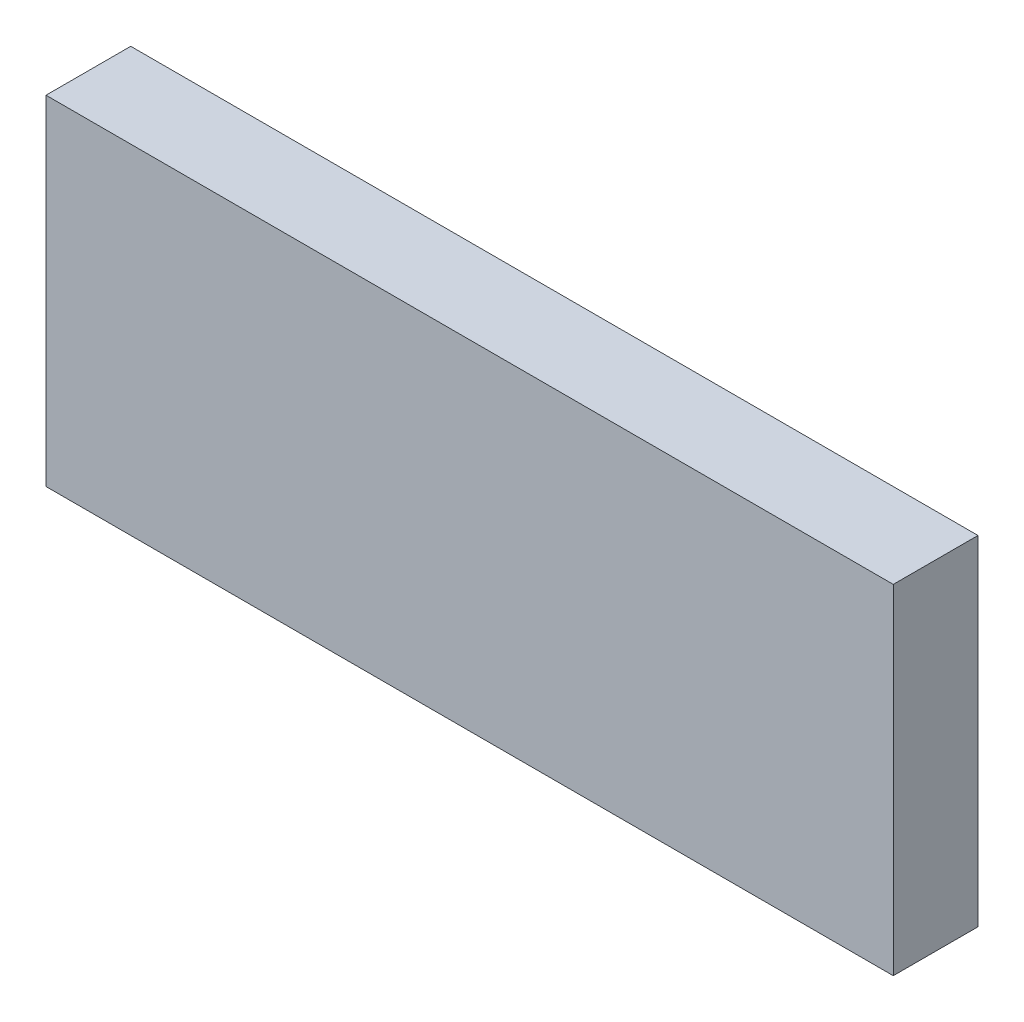
SolidWorks part; units mm, degrees
ref_plane "Front Plane" through (0, 0, 0) normal (0, 0, 1) x (1, 0, 0)
ref_plane "Top Plane" through (0, 0, 0) normal (0, 1, 0) x (1, 0, 0)
ref_plane "Right Plane" through (0, 0, 0) normal (1, 0, 0) x (0, 0, -1)
sketch "Sketch2" plane through (0, 0, 0) normal (0, 0, 1) x (1, 0, 0)
  line L1 (0, 0) -> (50, 0)
  line L2 (0, 0) -> (0, -20)
  line L3 (0, -20) -> (50, -20)
  line L4 (50, 0) -> (50, -20)
extrude "Boss-Extrude1" add sketch "Sketch2" along normal blind 5
